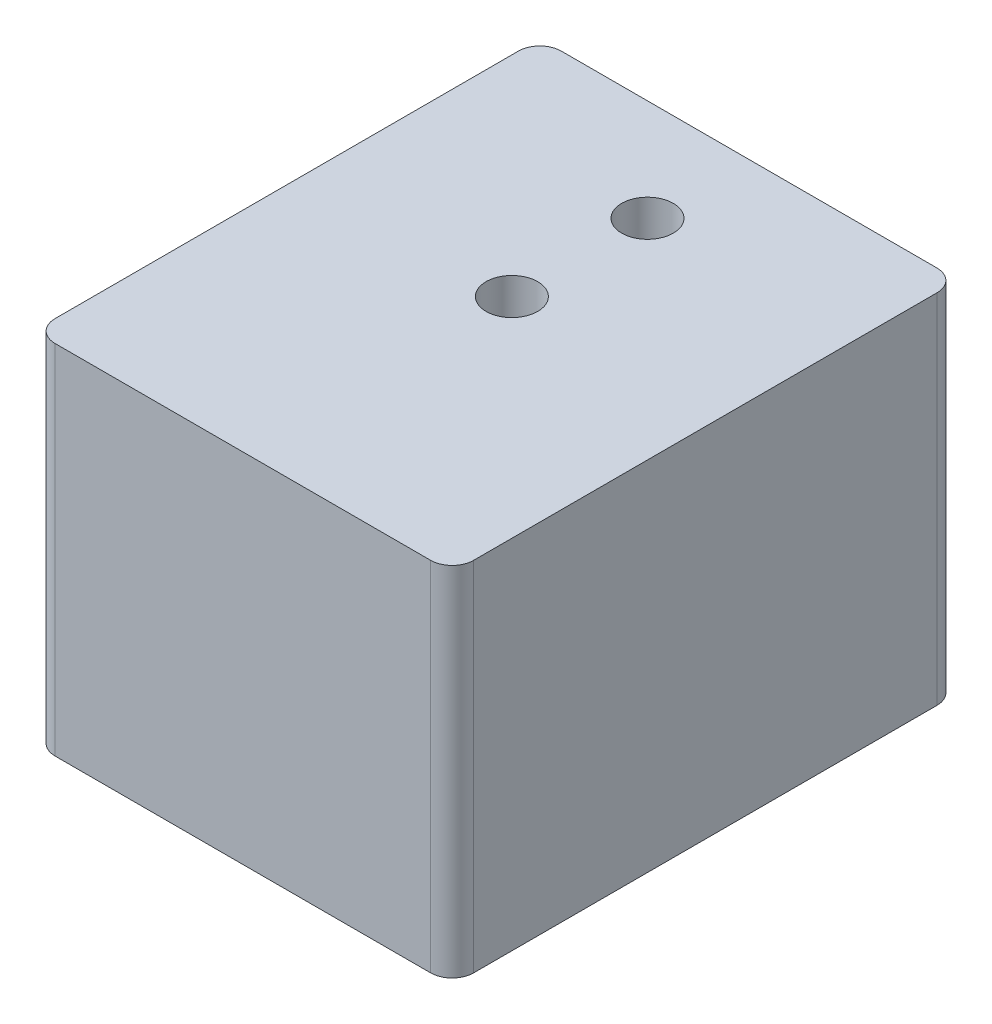
SolidWorks part; units mm, degrees
material "Nylon 101"
ref_plane "Front Plane" through (0, 0, 0) normal (0, 0, 1) x (1, 0, 0)
ref_plane "Top Plane" through (0, 0, 0) normal (0, 1, 0) x (1, 0, 0)
ref_plane "Right Plane" through (0, 0, 0) normal (1, 0, 0) x (0, 0, -1)
sketch "Sketch1" plane through (0, 0, 0) normal (0, 1, 0) x (1, 0, 0)
  line L0 (12.35, 0) -> (12.35, 29.875) construction
  line L1 (0, 0) -> (24.7, 0)
  line L2 (0, 0) -> (0, 29.875)
  line L3 (0, 29.875) -> (24.7, 29.875)
  line L4 (24.7, 0) -> (24.7, 29.875)
  circle A0 centre (12.35, 15.875) radius 1.524
  circle A1 centre (12.35, 23.875) radius 1.524
  dimension "D4" = 3.048
  dimension "D1" = 24.7
  dimension "D2" = 29.875
  dimension "D3" = 8
  dimension "D5" = 6
extrude "Boss-Extrude1" add sketch "Sketch1" along normal blind 21.082
fillet "Fillet1" radius 1.27 4 edges at (0, 10.541, -29.875) (24.7, 10.541, -29.875) (24.7, 10.541, 0) (0, 10.541, 0)
equation "\"D1@Sketch1\"=24.7mm"
equation "\"D2@Sketch1\"=27.875mm+2mm"
equation "\"D3@Sketch1\"=8mm"
equation "\"D5@Sketch1\"=6mm"
